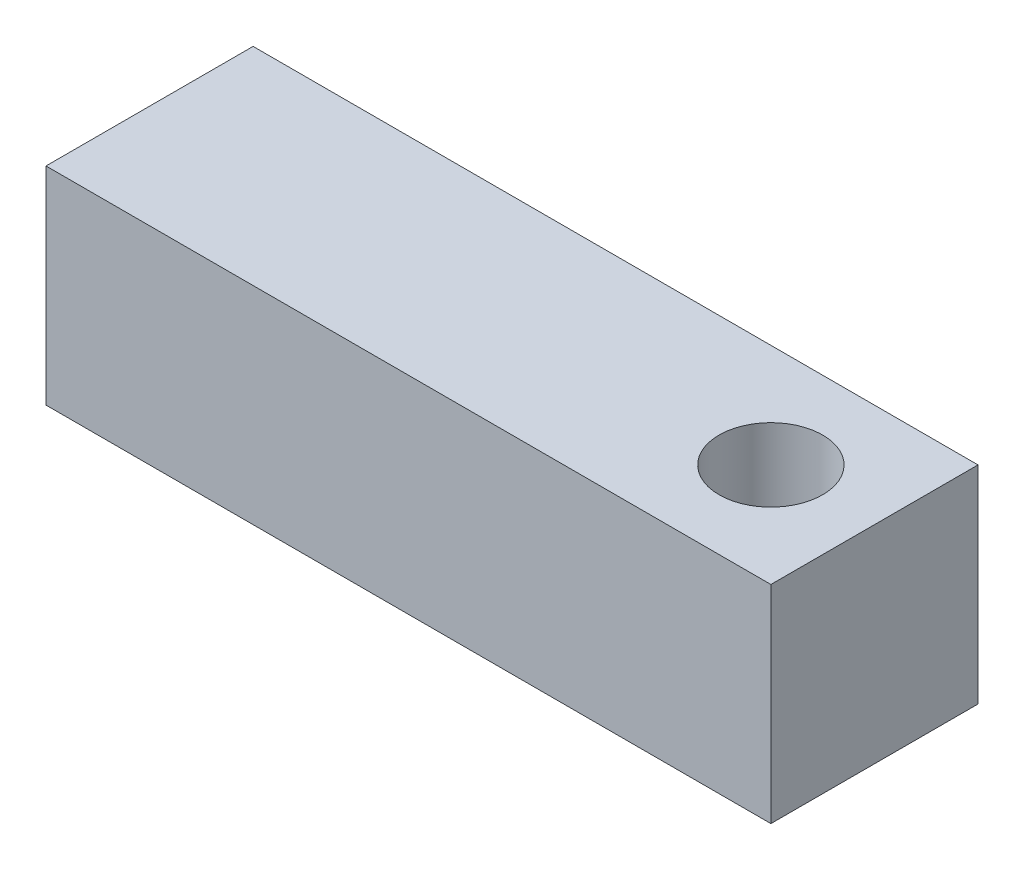
SolidWorks part; units mm, degrees
ref_plane "Front Plane" through (0, 0, 0) normal (0, 0, 1) x (1, 0, 0)
ref_plane "Top Plane" through (0, 0, 0) normal (0, 1, 0) x (1, 0, 0)
ref_plane "Right Plane" through (0, 0, 0) normal (1, 0, 0) x (0, 0, -1)
sketch "Sketch1" plane through (0, 0, 0) normal (0, 1, 0) x (1, 0, 0)
  line L1 (-14.4605, 0) -> (74.4395, 0)
  line L2 (-14.4605, 0) -> (-14.4605, 25.4)
  line L3 (-14.4605, 25.4) -> (74.4395, 25.4)
  line L4 (74.4395, 0) -> (74.4395, 25.4)
  circle A0 centre (61.7395, 12.7) radius 6.35
  dimension "D3" = 12.7
  dimension "D1" = 88.9
  dimension "D2" = 25.4
  dimension "D4" = 12.7
extrude "Boss-Extrude1" add sketch "Sketch1" along normal blind 25.4
ref_plane "Plane1" through (74.4395, 0, 0) normal (1, 0, 0) x (0, 0, -1)
